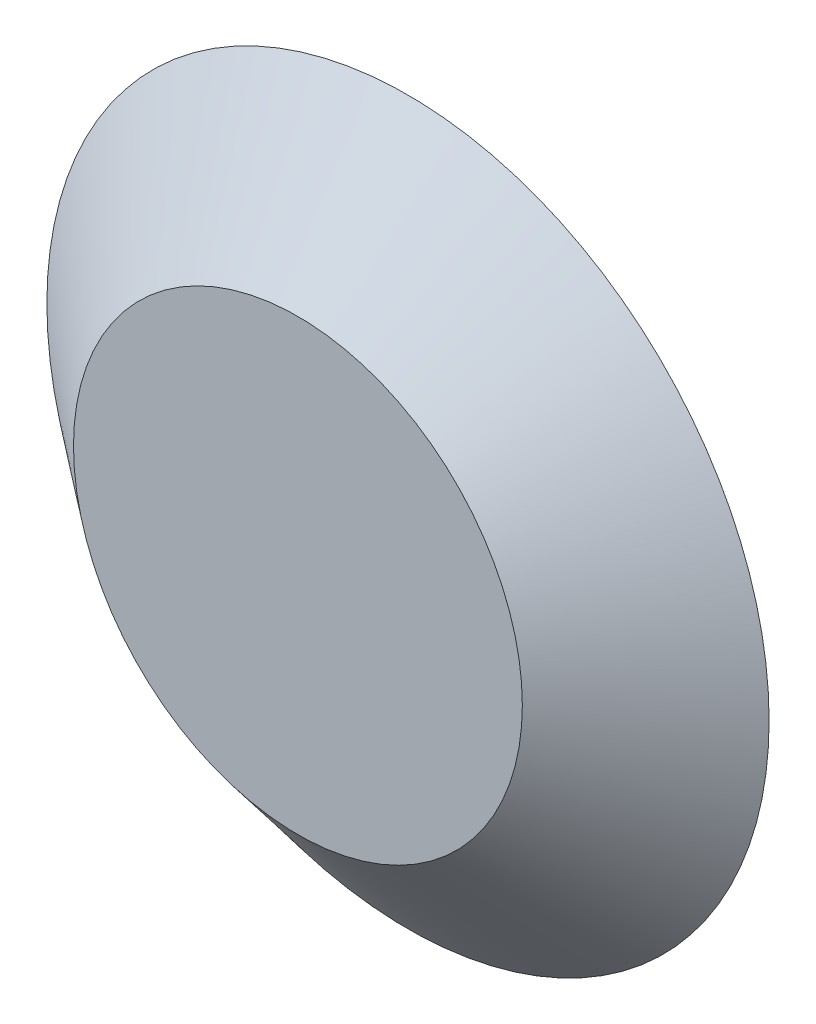
SolidWorks part; units mm, degrees
material "Bismuth"
ref_plane "Front" through (0, 0, 0) normal (0, 0, 1) x (1, 0, 0)
ref_plane "Top" through (0, 0, 0) normal (0, 1, 0) x (1, 0, 0)
ref_plane "Right" through (0, 0, 0) normal (1, 0, 0) x (0, 0, -1)
sketch "Sketch1" plane through (0, 0, 0) normal (0, 0, 1) x (1, 0, 0)
  circle A0 centre (0, 0) radius 133.5
extrude "Boss-Extrude1" add sketch "Sketch1" along normal blind 40.7 draft 51.15
